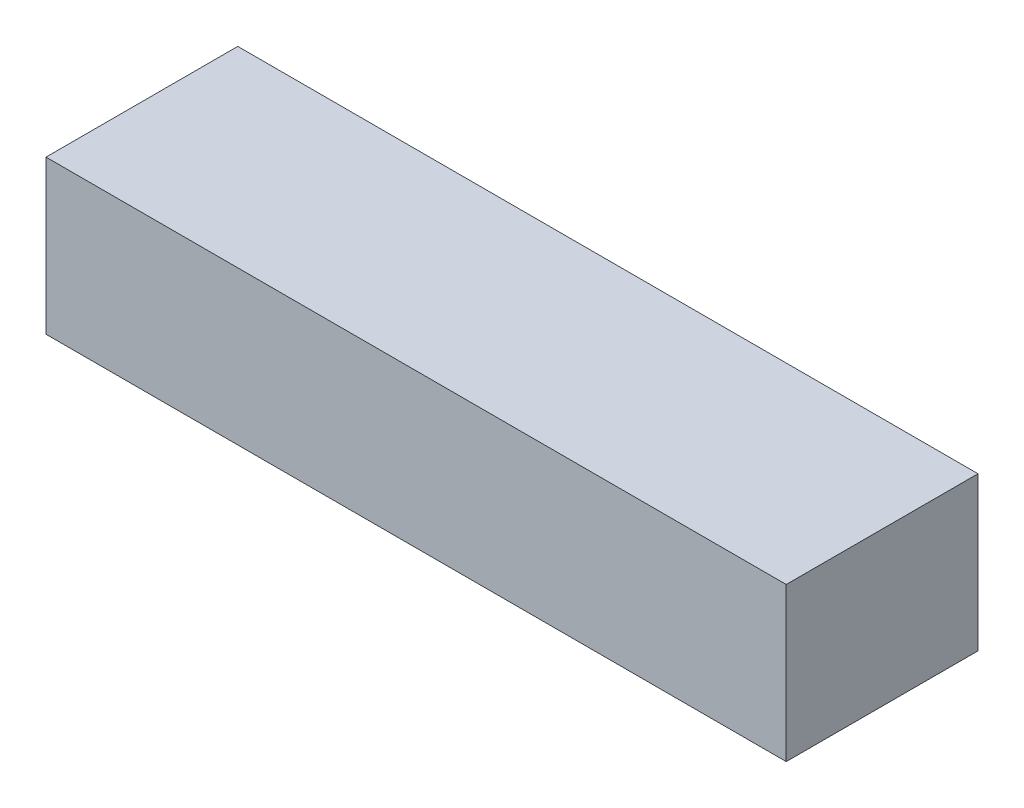
SolidWorks part; units mm, degrees
ref_plane "Front Plane" through (0, 0, 0) normal (0, 0, 1) x (1, 0, 0)
ref_plane "Top Plane" through (0, 0, 0) normal (0, 1, 0) x (1, 0, 0)
ref_plane "Right Plane" through (0, 0, 0) normal (1, 0, 0) x (0, 0, -1)
sketch "Sketch1" plane through (0, 0, 0) normal (0, 1, 0) x (1, 0, 0)
  line L0 (-17.6, 8) -> (-1.6, 8)
  line L1 (-38.6, -10) -> (38.6, -10)
  line L2 (-38.6, -10) -> (-38.6, 10)
  line L3 (-38.6, 10) -> (38.6, 10)
  line L4 (38.6, -10) -> (38.6, 10)
  line L5 (-38.6, -10) -> (38.6, 10) construction
  line L6 (-38.6, 10) -> (38.6, -10) construction
  line L7 (-36.6, 8) -> (-20.6, 8)
  line L8 (-36.6, 8) -> (-36.6, -8)
  line L9 (-36.6, -8) -> (-20.6, -8)
  line L10 (-20.6, 8) -> (-20.6, -8)
  line L11 (-36.6, 8) -> (-20.6, -8) construction
  line L12 (-36.6, -8) -> (-20.6, 8) construction
  line L13 (-17.6, 8) -> (-17.6, -8)
  line L14 (-17.6, -8) -> (-1.6, -8)
  line L15 (-1.6, 8) -> (-1.6, -8)
  line L16 (1.4, 8) -> (17.4, 8)
  line L17 (1.4, 8) -> (1.4, -8)
  line L18 (1.4, -8) -> (17.4, -8)
  line L19 (17.4, 8) -> (17.4, -8)
  line L20 (20.4, 8) -> (36.4, 8)
  line L21 (20.4, 8) -> (20.4, -8)
  line L22 (20.4, -8) -> (36.4, -8)
  line L23 (36.4, 8) -> (36.4, -8)
  point P0 (0, 0)
  point P6 (-28.6, 0)
  dimension "D1" = 20
  dimension "D2" = 77.2
  dimension "D3" = 16
  dimension "D4" = 16
  dimension "D5" = 2
  dimension "D6" = 4
extrude "Boss-Extrude1" add sketch "Sketch1" along normal blind 14
sketch "Sketch2" plane through (0, 14, 0) normal (0, 1, 0) x (1, 0, 0)
  line L1 (-38.6, 10) -> (38.6, 10)
  line L2 (-38.6, 10) -> (-38.6, -10)
  line L3 (-38.6, -10) -> (38.6, -10)
  line L4 (38.6, 10) -> (38.6, -10)
extrude "Boss-Extrude2" add sketch "Sketch2" along normal blind 2
